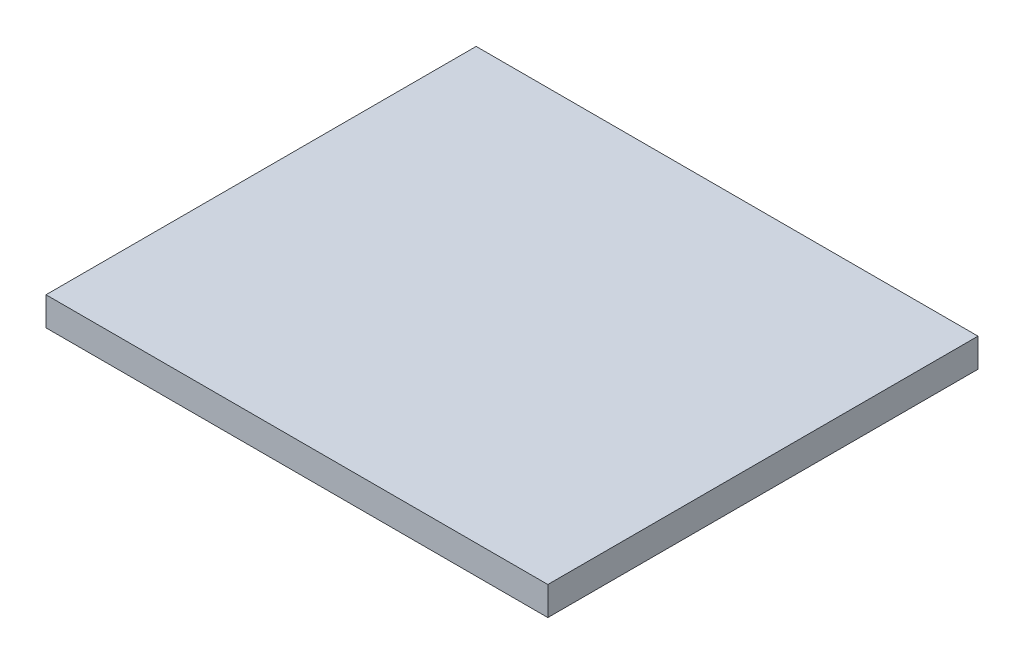
SolidWorks part; units mm, degrees
ref_plane "Front Plane" through (0, 0, 0) normal (0, 0, 1) x (1, 0, 0)
ref_plane "Top Plane" through (0, 0, 0) normal (0, 1, 0) x (1, 0, 0)
ref_plane "Right Plane" through (0, 0, 0) normal (1, 0, 0) x (0, 0, -1)
sketch "Sketch1" plane through (0, 0, 0) normal (0, 1, 0) x (1, 0, 0)
  line L1 (0, 0) -> (-350, 0)
  line L2 (0, 0) -> (0, 300)
  line L3 (0, 300) -> (-350, 300)
  line L4 (-350, 0) -> (-350, 300)
  dimension "D1" = 350
  dimension "D2" = 300
extrude "Boss-Extrude1" add sketch "Sketch1" along normal blind 20
